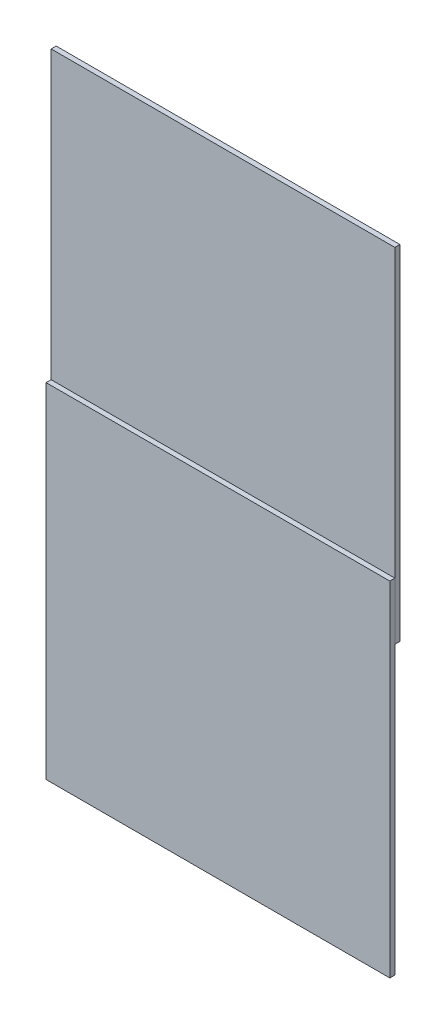
SolidWorks part; units mm, degrees
ref_plane "Ebene vorne" through (0, 0, 0) normal (0, 0, 1) x (1, 0, 0)
ref_plane "Ebene oben" through (0, 0, 0) normal (0, 1, 0) x (1, 0, 0)
ref_plane "Ebene rechts" through (0, 0, 0) normal (1, 0, 0) x (0, 0, -1)
sketch "Skizze2" plane through (0, 0, 0) normal (0, 0, 1) x (1, 0, 0)
  line L1 (0, 0) -> (150, 0)
  line L2 (0, 0) -> (0, -150)
  line L3 (0, -150) -> (150, -150)
  line L4 (150, 0) -> (150, -150)
  dimension "D1" = 150
  dimension "D2" = 150
extrude "Aufsatz-Linear austragen1" add sketch "Skizze2" along normal blind 2.2
sketch "Skizze3" plane through (0, 0, 0) normal (0, 0, -1) x (-1, 0, 0)
  line L0 (0, 0) -> (0, -150) construction
  line L1 (0, -25) -> (-150, -25)
  line L2 (0, -25) -> (0, 125)
  line L3 (0, 125) -> (-150, 125)
  line L4 (-150, -25) -> (-150, 125)
  line L5 (-150, 0) -> (0, 0) construction
  dimension "D1" = 150
  dimension "D2" = 25
extrude "Aufsatz-Linear austragen3" add sketch "Skizze3" along normal blind 2.2 separate body
sketch "Skizze5" plane through (0, -25, 0) normal (0, -1, 0) x (-1, 0, 0)
  line L0 (-150, 2.2) -> (0, 2.2) construction
  circle A0 centre (-92.4059, 14.7) radius 12.5
  dimension "D1" = 25
  dimension "D2" = 12.5
extrude "Aufsatz-Linear austragen4" add sketch "Skizze5" against normal blind 25 separate body
